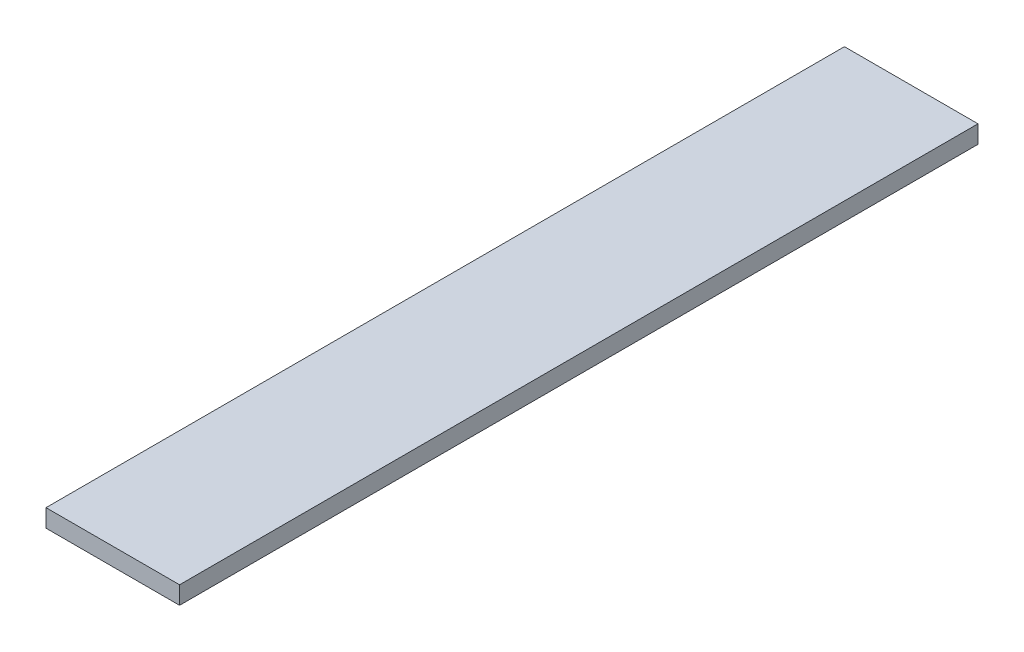
SolidWorks part; units mm, degrees
ref_plane "Front Plane" through (0, 0, 0) normal (0, 0, 1) x (1, 0, 0)
ref_plane "Top Plane" through (0, 0, 0) normal (0, 1, 0) x (1, 0, 0)
ref_plane "Right Plane" through (0, 0, 0) normal (1, 0, 0) x (0, 0, -1)
sketch "Sketch1" plane through (0, 0, 0) normal (0, 1, 0) x (1, 0, 0)
  line L1 (0, 0) -> (285.75, 0)
  line L2 (0, 0) -> (0, -1708.15)
  line L3 (0, -1708.15) -> (285.75, -1708.15)
  line L4 (285.75, 0) -> (285.75, -1708.15)
extrude "Boss-Extrude1" add sketch "Sketch1" along normal blind 38.1
